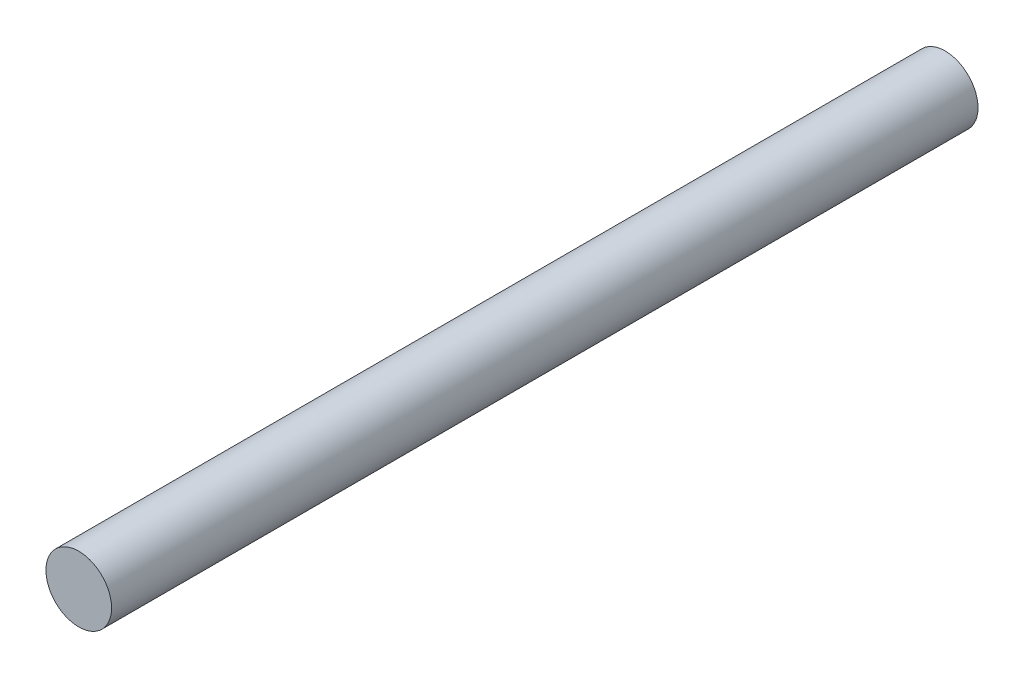
SolidWorks part; units mm, degrees
ref_plane "Front Plane" through (0, 0, 0) normal (0, 0, 1) x (1, 0, 0)
ref_plane "Top Plane" through (0, 0, 0) normal (0, 1, 0) x (1, 0, 0)
ref_plane "Right Plane" through (0, 0, 0) normal (1, 0, 0) x (0, 0, -1)
sketch "Sketch1" plane through (0, 0, 0) normal (0, 1, 0) x (1, 0, 0)
  line L0 (0, -53.7838) -> (0, 80.9461) construction
  line L1 (0, 33) -> (2.5, 33)
  line L2 (2.5, 33) -> (2.5, -33)
  line L3 (2.5, -33) -> (0, -33)
  line L4 (0, -33) -> (0, 33)
  dimension "D1" = 5
  dimension "D2" = 66
revolve "Revolve1" add sketch "Sketch1" angle 360 about L0
